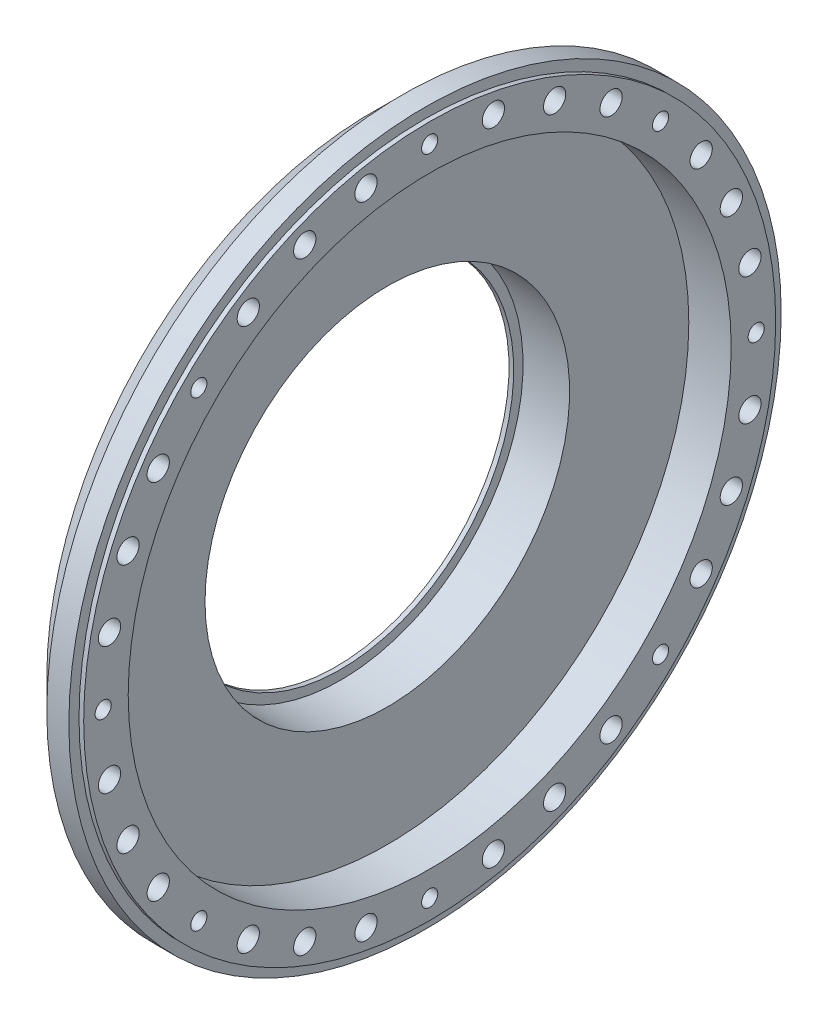
SolidWorks part; units mm, degrees
ref_plane "Front Plane" through (0, 0, 0) normal (0, 0, 1) x (1, 0, 0)
ref_plane "Top Plane" through (0, 0, 0) normal (0, 1, 0) x (1, 0, 0)
ref_plane "Right Plane" through (0, 0, 0) normal (1, 0, 0) x (0, 0, -1)
sketch "Sketch2" plane through (0, 0, 0) normal (0, 0, 1) x (1, 0, 0)
  line L0 (0, 0) -> (58.591, 0) construction
  line L2 (0, 0) -> (18.4, 0)
  line L3 (0, 0) -> (0, 2.5)
  line L4 (0, 2.5) -> (18.4, 2.5)
  line L5 (18.4, 0) -> (18.4, 2.5)
  line L6 (6.0094, 2.5) -> (6.0094, 6)
  line L11 (6.0094, 6) -> (9.9794, 6)
  line L16 (12.9794, 6) -> (12.9794, 3)
  line L17 (12.9794, 3) -> (13.6398, 3)
  line L18 (13.6398, 3) -> (13.6398, 2.5)
  line L19 (13.6398, 2.5) -> (6.0094, 2.5)
  line L22 (13.6398, 2.5) -> (16.1198, 2.5)
  line L23 (13.6398, 2.5) -> (13.6398, 4)
  line L24 (13.6398, 4) -> (16.1198, 4)
  line L25 (16.1198, 2.5) -> (16.1198, 4)
  line L27 (6.0094, 6) -> (9.9794, 6)
  line L28 (6.0094, 6) -> (6.0094, 9)
  line L29 (6.0094, 9) -> (9.9794, 9)
  line L30 (9.9794, 6) -> (9.9794, 9)
  line L31 (6.0094, 9) -> (6.0094, 8.25)
  line L32 (6.0094, 8.25) -> (5.0094, 8.25)
  line L33 (8.6609, 22.001) -> (8.6609, 12.476) construction
  line L34 (5.0094, 12.476) -> (12.3124, 12.476)
  line L35 (9.9794, 9) -> (12.3124, 9)
  line L36 (5.0094, 7.9375) -> (1.7709, 7.9375)
  line L37 (5.0094, 8.25) -> (5.0094, 12.476)
  line L38 (5.0094, 7.9375) -> (5.0094, 13.9365)
  line L39 (5.0094, 13.9365) -> (1.7709, 13.9365)
  line L40 (1.7709, 7.9375) -> (1.7709, 13.9365)
  line L41 (5.0094, 22.001) -> (12.3124, 22.001)
  line L42 (5.0094, 22.001) -> (5.0094, 30.1625)
  line L43 (5.0094, 30.1625) -> (12.3124, 30.1625)
  line L44 (12.3124, 22.001) -> (12.3124, 30.1625)
  line L49 (16.6398, 22.001) -> (16.6398, 7.5)
  line L51 (23.0198, 7.5) -> (23.0198, 6.5)
  line L54 (16.1198, 4) -> (13.6398, 4)
  line L56 (18.0398, 7.5) -> (23.0198, 7.5)
  line L57 (13.3124, 22.001) -> (16.6398, 22.001)
  line L58 (16.1198, 3.5) -> (20.0198, 3.5)
  line L59 (29.9098, 14) -> (26.9098, 11)
  line L60 (4.0094, 31.75) -> (18.0398, 31.75)
  line L61 (18.0398, 7.5) -> (23.0198, 7.5)
  line L62 (18.0398, 7.5) -> (18.0398, 12)
  line L63 (18.0398, 12) -> (23.0198, 12)
  line L64 (23.0198, 7.5) -> (23.0198, 12)
  line L65 (18.0398, 31.75) -> (18.0398, 12)
  line L66 (23.0198, 11) -> (26.9098, 11)
  line L67 (34.8098, 23) -> (31.3098, 19.5)
  line L68 (35.8098, 31) -> (38.7998, 33.99)
  line L69 (29.9098, 14) -> (29.9098, 15)
  line L70 (29.9098, 15) -> (22.9398, 15)
  line L71 (22.9398, 15) -> (21.0398, 15)
  line L72 (18.0398, 7.5) -> (16.6398, 7.5)
  line L73 (21.0398, 15) -> (21.0398, 43)
  line L74 (19.6115, 40) -> (9.6516, 40)
  line L75 (9.6516, 40) -> (4.0094, 40)
  line L76 (21.0398, 43) -> (19.6115, 43)
  line L77 (22.9398, 15) -> (29.9098, 15)
  line L78 (22.9398, 15) -> (22.9398, 21)
  line L79 (22.9398, 21) -> (29.9098, 21)
  line L80 (29.9098, 15) -> (29.9098, 21)
  line L81 (9.6516, 40) -> (19.6115, 40)
  line L82 (9.6516, 40) -> (9.6516, 50)
  line L83 (9.6516, 50) -> (19.6115, 50)
  line L84 (19.6115, 40) -> (19.6115, 50)
  line L85 (4.0094, 40) -> (4.0094, 31.75)
  line L86 (12.9794, 3) -> (12.9794, 2.5)
  line L87 (31.3098, 19.5) -> (29.9098, 19.5)
  line L88 (21.4694, 63.5) -> (21.4694, 51.308)
  line L89 (21.4694, 63.5) -> (25.9398, 63.5)
  line L90 (25.9398, 63.5) -> (25.9398, 25)
  line L91 (27.8398, 25) -> (25.9398, 25)
  line L92 (9.6516, 48) -> (8.2233, 48)
  line L93 (8.2233, 48) -> (8.2233, 53.476)
  line L94 (8.2233, 53.476) -> (19.6115, 53.476)
  line L95 (19.6115, 53.476) -> (19.6115, 50)
  line L96 (13.9174, 63.001) -> (13.9174, 53.476) construction
  line L97 (8.2233, 63.001) -> (19.6115, 63.001)
  line L98 (8.2233, 63.001) -> (8.2233, 68.2625)
  line L99 (8.2233, 68.2625) -> (19.6115, 68.2625)
  line L100 (19.6115, 63.001) -> (19.6115, 68.2625)
  line L101 (12.9794, 6) -> (11.9794, 6)
  line L102 (8.2233, 44.825) -> (4.9848, 44.825)
  line L103 (8.2233, 44.825) -> (8.2233, 54.9365)
  line L104 (8.2233, 54.9365) -> (4.9848, 54.9365)
  line L106 (9.9794, 6) -> (10.8794, 6)
  line L107 (27.8398, 25) -> (34.8098, 25)
  line L108 (34.8098, 25) -> (34.8098, 23)
  line L109 (0, 0) -> (-2, 0)
  line L110 (0, 0) -> (0, 11)
  line L111 (27.8398, 25) -> (34.8098, 25)
  line L112 (27.8398, 25) -> (27.8398, 32.5)
  line L113 (27.8398, 32.5) -> (34.8098, 32.5)
  line L114 (34.8098, 25) -> (34.8098, 32.5)
  line L115 (35.8098, 31) -> (34.8098, 31)
  line L116 (27.8398, 32.5) -> (27.8398, 64.5)
  line L117 (20.5849, 74.025) -> (6.2499, 74.025)
  line L118 (6.2499, 74.025) -> (6.2499, 76.2)
  line L119 (38.7998, 47.29) -> (30.8398, 55.25)
  line L120 (0, 11) -> (-2, 11)
  line L121 (38.7998, 43.815) -> (30.8623, 43.815)
  line L123 (-4.8152, 69.85) -> (1.5348, 76.2)
  line L124 (38.7998, 47.29) -> (38.7998, 33.99)
  line L125 (-2, 0) -> (-2, 11)
  line L126 (38.7998, 37.465) -> (30.8623, 37.465)
  line L127 (30.8623, 43.815) -> (30.8623, 37.465)
  line L128 (6.0094, 2.5) -> (6.0094, 0)
  line L129 (-0.0152, 63.5) -> (-0.0152, 30)
  line L132 (4.9848, 63.5) -> (-0.0152, 63.5)
  line L136 (-1.8152, 30) -> (-11.7752, 30)
  line L138 (-13.7752, 25.4) -> (-2, 25.4)
  line L139 (-2, 25.4) -> (-2, 11.5)
  line L140 (27.8398, 64.5) -> (20.5849, 64.5)
  line L141 (-1.8152, 30) -> (-11.7752, 30)
  line L142 (-1.8152, 30) -> (-1.8152, 39)
  line L143 (-1.8152, 39) -> (-11.7752, 39)
  line L144 (-11.7752, 30) -> (-11.7752, 39)
  line L145 (20.5849, 64.5) -> (20.5849, 74.025)
  line L146 (-12.7752, 37) -> (-12.7752, 47.29)
  line L147 (-12.7752, 37) -> (-11.7752, 37)
  line L148 (30.8398, 55.25) -> (30.8398, 76.2)
  line L149 (11.9794, 6) -> (11.9794, 5.45)
  line L154 (-2, 11.5) -> (0.5, 11.5)
  line L155 (4.9848, 60.6197) -> (24.0348, 60.6197)
  line L160 (4.9848, 60.6197) -> (4.9848, 55.8572)
  line L161 (4.9848, 55.8572) -> (24.0348, 55.8572)
  line L166 (24.0348, 60.6197) -> (24.0348, 55.8572)
  line L167 (4.9848, 60.6197) -> (24.0348, 55.8572) construction
  line L172 (4.9848, 55.8572) -> (24.0348, 60.6197) construction
  line L173 (24.0348, 62.2072) -> (25.9398, 62.2072)
  line L174 (11.9794, 5.45) -> (10.8794, 5.45)
  line L175 (10.8794, 6) -> (10.8794, 5.45)
  line L176 (24.0348, 62.2072) -> (24.0348, 54.2697)
  line L177 (24.0348, 54.2697) -> (25.9398, 54.2697)
  line L178 (25.9398, 62.2072) -> (25.9398, 54.2697)
  line L179 (24.0348, 62.2072) -> (25.9398, 54.2697) construction
  line L180 (24.0348, 54.2697) -> (25.9398, 62.2072) construction
  line L181 (3, 19.6197) -> (15.7, 19.6197)
  line L182 (3, 19.6197) -> (3, 14.8572)
  line L183 (3, 14.8572) -> (15.7, 14.8572)
  line L184 (15.7, 19.6197) -> (15.7, 14.8572)
  line L185 (3, 19.6197) -> (15.7, 14.8572) construction
  line L186 (3, 14.8572) -> (15.7, 19.6197) construction
  line L187 (15.7, 21.2072) -> (16.6398, 21.2072)
  line L188 (15.7, 21.2072) -> (15.7, 13.2697)
  line L189 (15.7, 13.2697) -> (16.6398, 13.2697)
  line L190 (16.6398, 21.2072) -> (16.6398, 13.2697)
  line L191 (15.7, 21.2072) -> (16.6398, 13.2697) construction
  line L192 (15.7, 13.2697) -> (16.6398, 21.2072) construction
  line L193 (0.5, 11.5) -> (0.5, 6.9375)
  line L194 (0.5, 6.9375) -> (1.7709, 6.9375)
  line L195 (23.0198, 6.5) -> (20.0198, 3.5)
  line L196 (4.9848, 63.5) -> (4.9848, 54.9365)
  line L197 (3, 43.825) -> (4.9848, 43.825)
  line L198 (1.7709, 6.9375) -> (1.7709, 7.9375)
  line L199 (6.0094, 0) -> (12.9794, 0)
  line L200 (12.9794, 0) -> (12.9794, 2.5)
  line L201 (18.0398, 31.75) -> (18.0398, 35.875)
  line L202 (18.0398, 35.875) -> (21.0398, 35.875)
  line L203 (30.8398, 76.2) -> (6.2499, 76.2)
  line L204 (2.8049, 69.85) -> (7.2499, 69.85) construction
  line L205 (7.2499, 67.4688) -> (26.2999, 67.4688)
  line L206 (7.2499, 74.025) -> (7.2499, 64.5)
  line L207 (7.2499, 64.5) -> (-1.8152, 64.5)
  line L208 (-1.8152, 64.5) -> (-1.8152, 39)
  line L209 (-12.7752, 47.29) -> (-4.8152, 55.25)
  line L210 (-4.8152, 55.25) -> (-4.8152, 69.85)
  line L211 (7.2499, 67.4688) -> (7.2499, 72.2312)
  line L212 (7.2499, 72.2312) -> (26.2999, 72.2313)
  line L213 (26.2999, 67.4688) -> (26.2999, 72.2313)
  line L214 (26.2999, 73.8187) -> (30.8398, 73.8187)
  line L215 (26.2999, 73.8187) -> (26.2999, 65.8813)
  line L216 (26.2999, 65.8813) -> (30.8398, 65.8813)
  line L217 (30.8398, 73.8187) -> (30.8398, 65.8813)
  line L218 (2.8049, 72.2313) -> (25.0299, 72.2313)
  line L219 (2.8049, 72.2313) -> (2.8049, 67.4687)
  line L220 (2.8049, 67.4687) -> (25.0299, 67.4687)
  line L221 (25.0299, 72.2313) -> (25.0299, 67.4687)
  line L222 (25.0299, 69.85) -> (20.5849, 69.85) construction
  line L223 (21.4694, 51.308) -> (22.9398, 51.308)
  line L224 (22.9398, 51.308) -> (22.9398, 21)
  line L225 (13.6398, 4) -> (13.6398, 12.2697)
  line L226 (13.6398, 12.2697) -> (13.3124, 12.2697)
  line L227 (13.3124, 12.2697) -> (13.3124, 22.001)
  line L228 (12.3124, 9) -> (12.3124, 12.476)
  line L229 (-1.8152, 30) -> (-0.0152, 30)
  line L230 (8.2233, 65.6317) -> (2.8049, 65.6317) construction
  line L231 (19.6115, 65.6317) -> (25.0299, 65.6317) construction
  line L232 (1.5348, 76.2) -> (6.2499, 76.2)
  line L233 (-11.7752, 30) -> (-13.7752, 30)
  line L234 (-13.7752, 30) -> (-13.7752, 25.4)
  line L235 (3, 13.9365) -> (3, 43.825)
  line L236 (4.9848, 54.9365) -> (4.9848, 44.825)
  line L237 (4.9848, 43.825) -> (4.9848, 44.825)
  circle A0 centre (26.8898, 25.95) radius 0.95
  circle A1 centre (21.9898, 15.95) radius 0.95
  circle A2 centre (17.3398, 8.2) radius 0.7
  circle A3 centre (10.4294, 6.45) radius 0.45
  circle A4 centre (-0.9152, 30.9) radius 0.9
  point P7 (24.9873, 58.2385)
  point P131 (16.1699, 17.2385)
  point P135 (14.5098, 58.2385)
  point P146 (9.35, 17.2385)
sketch "Sketch3" plane through (0, 0, 0) normal (1, 0, 0) x (0, 0, -1)
  line L0 (0, 0) -> (0, 69.85) construction
  line L1 (0, 0) -> (13.6271, 68.5079) construction
  line L2 (0, 0) -> (0, 58.2385) construction
  line L3 (0, 0) -> (50.436, 29.1192) construction
  line L4 (0, 0) -> (0, 31.75) construction
  line L5 (0, 0) -> (12.1502, 29.3332) construction
  line L6 (0, 0) -> (0, 17.2385) construction
  line L7 (0, 0) -> (14.929, 8.6192) construction
  line L8 (0, 0) -> (0, 58.2385) construction
  line L9 (0, 0) -> (50.436, 29.1192) construction
  line L10 (0, 0) -> (5.9583, 29.9542) construction
  line L11 (0, 0) -> (16.9677, 25.394) construction
  circle A0 centre (0, 0) radius 69.85 construction
  circle A1 centre (0, 0) radius 58.2385 construction
  circle A2 centre (0, 0) radius 31.75 construction
  circle A3 centre (0, 0) radius 17.2385 construction
  circle A4 centre (0, 69.85) radius 3.175
  circle A5 centre (0, 58.2385) radius 4.7625
  circle A6 centre (0, 31.75) radius 3.175
  circle A7 centre (0, 17.2385) radius 4.7625
  circle A8 centre (13.6271, 68.5079) radius 3.175
  circle A9 centre (26.7304, 64.533) radius 3.175
  circle A10 centre (38.8066, 58.0782) radius 3.175
  circle A11 centre (49.3914, 49.3914) radius 3.175
  circle A12 centre (58.0782, 38.8066) radius 3.175
  circle A13 centre (64.533, 26.7304) radius 3.175
  circle A14 centre (68.5079, 13.6271) radius 3.175
  circle A15 centre (69.85, 0) radius 3.175
  circle A16 centre (68.5079, -13.6271) radius 3.175
  circle A17 centre (64.533, -26.7304) radius 3.175
  circle A18 centre (58.0782, -38.8066) radius 3.175
  circle A19 centre (49.3914, -49.3914) radius 3.175
  circle A20 centre (38.8066, -58.0782) radius 3.175
  circle A21 centre (26.7304, -64.533) radius 3.175
  circle A22 centre (13.6271, -68.5079) radius 3.175
  circle A23 centre (0, -69.85) radius 3.175
  circle A24 centre (-13.6271, -68.5079) radius 3.175
  circle A25 centre (-26.7304, -64.533) radius 3.175
  circle A26 centre (-38.8066, -58.0782) radius 3.175
  circle A27 centre (-49.3914, -49.3914) radius 3.175
  circle A28 centre (-58.0782, -38.8066) radius 3.175
  circle A29 centre (-64.533, -26.7304) radius 3.175
  circle A30 centre (-68.5079, -13.6271) radius 3.175
  circle A31 centre (-69.85, 0) radius 3.175
  circle A32 centre (-68.5079, 13.6271) radius 3.175
  circle A33 centre (-64.533, 26.7304) radius 3.175
  circle A34 centre (-58.0782, 38.8066) radius 3.175
  circle A35 centre (-49.3914, 49.3914) radius 3.175
  circle A36 centre (-38.8066, 58.0782) radius 3.175
  circle A37 centre (-26.7304, 64.533) radius 3.175
  circle A38 centre (-13.6271, 68.5079) radius 3.175
  circle A47 centre (50.436, 29.1192) radius 4.7625
  circle A48 centre (50.436, -29.1192) radius 4.7625
  circle A49 centre (0, -58.2385) radius 4.7625
  circle A50 centre (-50.436, -29.1192) radius 4.7625
  circle A51 centre (-50.436, 29.1192) radius 4.7625
  circle A58 centre (12.1502, 29.3332) radius 3.175
  circle A59 centre (22.4506, 22.4506) radius 3.175
  circle A60 centre (29.3332, 12.1502) radius 3.175
  circle A61 centre (31.75, 0) radius 3.175
  circle A62 centre (29.3332, -12.1502) radius 3.175
  circle A63 centre (22.4506, -22.4506) radius 3.175
  circle A64 centre (12.1502, -29.3332) radius 3.175
  circle A65 centre (0, -31.75) radius 3.175
  circle A66 centre (-12.1502, -29.3332) radius 3.175
  circle A67 centre (-22.4506, -22.4506) radius 3.175
  circle A68 centre (-29.3332, -12.1502) radius 3.175
  circle A69 centre (-31.75, 0) radius 3.175
  circle A70 centre (-29.3332, 12.1502) radius 3.175
  circle A71 centre (-22.4506, 22.4506) radius 3.175
  circle A72 centre (14.929, 8.6192) radius 4.7625
  circle A73 centre (14.929, -8.6192) radius 4.7625
  circle A74 centre (0, -17.2385) radius 4.7625
  circle A75 centre (-14.929, -8.6192) radius 4.7625
  circle A76 centre (-14.929, 8.6192) radius 4.7625
  circle A77 centre (0, 0) radius 50
  circle A78 centre (0, 0) radius 9
  circle A79 centre (-12.1502, 29.3332) radius 3.175
  circle A80 centre (0, 0) radius 76.2
  circle A81 centre (0, 0) radius 74.025
  circle A82 centre (0, 69.85) radius 3.9687
  circle A83 centre (49.3914, 49.3914) radius 3.9687
  circle A84 centre (69.85, 0) radius 3.9688
  circle A85 centre (49.3914, -49.3914) radius 3.9687
  circle A86 centre (0, -69.85) radius 3.9687
  circle A87 centre (-49.3914, -49.3914) radius 3.9687
  circle A88 centre (-69.85, 0) radius 3.9688
  circle A89 centre (-49.3914, 49.3914) radius 3.9687
  circle A90 centre (0, 69.85) radius 2.3812
  circle A91 centre (13.6271, 68.5079) radius 2.3812
  circle A92 centre (26.7304, 64.533) radius 2.3813
  circle A93 centre (38.8066, 58.0782) radius 2.3812
  circle A94 centre (49.3914, 49.3914) radius 2.3812
  circle A95 centre (58.0782, 38.8066) radius 2.3812
  circle A96 centre (64.533, 26.7304) radius 2.3813
  circle A97 centre (68.5079, 13.6271) radius 2.3813
  circle A98 centre (69.85, 0) radius 2.3813
  circle A99 centre (68.5079, -13.6271) radius 2.3813
  circle A100 centre (64.533, -26.7304) radius 2.3813
  circle A101 centre (58.0782, -38.8066) radius 2.3812
  circle A102 centre (49.3914, -49.3914) radius 2.3812
  circle A103 centre (38.8066, -58.0782) radius 2.3812
  circle A104 centre (26.7304, -64.533) radius 2.3813
  circle A105 centre (13.6271, -68.5079) radius 2.3812
  circle A106 centre (0, -69.85) radius 2.3812
  circle A107 centre (-13.6271, -68.5079) radius 2.3812
  circle A108 centre (-26.7304, -64.533) radius 2.3813
  circle A109 centre (-38.8066, -58.0782) radius 2.3812
  circle A110 centre (-49.3914, -49.3914) radius 2.3812
  circle A111 centre (-58.0782, -38.8066) radius 2.3812
  circle A112 centre (-64.533, -26.7304) radius 2.3812
  arc A113 (3.0399, 30.8338) -> (8.9911, 29.65) centre (5.9583, 29.9542) cw
  arc A114 (14.6081, 27.3234) -> (19.6532, 23.9523) centre (16.9677, 25.394) cw
  arc A115 (23.9523, 19.6532) -> (27.3234, 14.6081) centre (25.394, 16.9677) cw
  arc A116 (29.65, 8.9911) -> (30.8338, 3.0399) centre (29.9542, 5.9583) cw
  arc A117 (30.8338, -3.0399) -> (29.65, -8.9911) centre (29.9542, -5.9583) cw
  arc A118 (27.3234, -14.6081) -> (23.9523, -19.6532) centre (25.394, -16.9677) cw
  arc A119 (19.6532, -23.9523) -> (14.6081, -27.3234) centre (16.9677, -25.394) cw
  arc A120 (8.9911, -29.65) -> (3.0399, -30.8338) centre (5.9583, -29.9542) cw
  arc A121 (-3.0399, -30.8338) -> (-8.9911, -29.65) centre (-5.9583, -29.9542) cw
  arc A122 (-14.6081, -27.3234) -> (-19.6532, -23.9523) centre (-16.9677, -25.394) cw
  arc A123 (-23.9523, -19.6532) -> (-27.3234, -14.6081) centre (-25.394, -16.9677) cw
  arc A124 (-29.65, -8.9911) -> (-30.8338, -3.0399) centre (-29.9542, -5.9583) cw
  arc A125 (-30.8338, 3.0399) -> (-29.65, 8.9911) centre (-29.9542, 5.9583) cw
  arc A126 (-27.3234, 14.6081) -> (-23.9523, 19.6532) centre (-25.394, 16.9677) cw
  arc A127 (-19.6532, 23.9523) -> (-14.6081, 27.3234) centre (-16.9677, 25.394) cw
  arc A128 (-8.9911, 29.65) -> (-3.0399, 30.8338) centre (-5.9583, 29.9542) cw
  arc A129 (26.9875, 0) -> (26.9932, 0.1932) centre (30.2705, 0) cw
  arc A130 (65.0988, 0.2771) -> (65.0875, 0) centre (68.4964, 0) ccw
  circle A131 centre (1.5875, 0) radius 40
  circle A132 centre (1.5875, 0) radius 2.5
  circle A133 centre (1.5875, 0) radius 3
  circle A134 centre (1.5875, 0) radius 43
  circle A135 centre (-68.5079, -13.6271) radius 2.3813
  circle A136 centre (-69.85, 0) radius 2.3813
  circle A137 centre (-68.5079, 13.6271) radius 2.3813
  circle A138 centre (-64.533, 26.7304) radius 2.3812
  circle A139 centre (-58.0782, 38.8066) radius 2.3812
  circle A140 centre (-49.3914, 49.3914) radius 2.3812
  circle A141 centre (-38.8066, 58.0782) radius 2.3812
  circle A142 centre (-26.7304, 64.533) radius 2.3813
  circle A143 centre (-13.6271, 68.5079) radius 2.3812
  circle A144 centre (0, 58.2385) radius 2.3812
  circle A145 centre (0, 58.2385) radius 3.9688
  circle A146 centre (50.436, 29.1192) radius 3.9688
  circle A147 centre (50.436, 29.1192) radius 2.3813
  circle A148 centre (50.436, -29.1192) radius 3.9687
  circle A149 centre (50.436, -29.1192) radius 2.3812
  circle A150 centre (0, -58.2385) radius 3.9687
  circle A151 centre (0, -58.2385) radius 2.3812
  circle A152 centre (-50.436, -29.1192) radius 3.9687
  circle A153 centre (-50.436, -29.1192) radius 2.3812
  circle A154 centre (-50.436, 29.1192) radius 3.9687
  circle A155 centre (-50.436, 29.1192) radius 2.3812
  spline S1 degree 4 number of poles 499 (26.9875, 0) -> (26.9932, 0.1932)
  spline S3 degree 4 number of poles 617 (65.0875, 0) -> (65.0988, 0.2771)
  point P116 (0, 0)
  point P225 (0, 0)
sketch "Sketch4" plane through (0, 0, 0) normal (0, 0, 1) x (1, 0, 0)
  line L0 (20.5849, 74.025) -> (6.2499, 74.025) construction
  line L1 (6.2499, 74.025) -> (6.2499, 76.2) construction
  line L2 (7.2499, 74.025) -> (7.2499, 64.5) construction
  line L3 (7.2499, 64.5) -> (-1.8152, 64.5) construction
  line L4 (-1.8152, 64.5) -> (-1.8152, 39) construction
  line L5 (-11.7752, 30) -> (-11.7752, 39) construction
  line L6 (-1.8152, 39) -> (-11.7752, 39) construction
  line L7 (-12.7752, 37) -> (-11.7752, 37) construction
  line L8 (-12.7752, 37) -> (-12.7752, 47.29) construction
  line L9 (-12.7752, 47.29) -> (-4.8152, 55.25) construction
  line L10 (-4.8152, 55.25) -> (-4.8152, 69.85) construction
  line L12 (7.2499, 74.025) -> (6.2499, 74.025)
  line L13 (6.2499, 74.025) -> (6.2499, 76.2)
  line L14 (7.2499, 74.025) -> (7.2499, 64.5)
  line L15 (7.2499, 64.5) -> (-1.8152, 64.5)
  line L16 (-1.8152, 64.5) -> (-1.8152, 39)
  line L17 (-11.7752, 37) -> (-11.7752, 39)
  line L18 (-1.8152, 39) -> (-11.7752, 39)
  line L19 (-12.7752, 37) -> (-11.7752, 37)
  line L20 (-12.7752, 37) -> (-12.7752, 47.29)
  line L21 (-12.7752, 47.29) -> (-4.8152, 55.25)
  line L22 (-4.8152, 55.25) -> (-4.8152, 69.85)
  line L24 (-4.8152, 69.85) -> (1.5348, 76.2) construction
  line L25 (1.5348, 76.2) -> (6.2499, 76.2) construction
  line L26 (-4.8152, 69.85) -> (1.5348, 76.2)
  line L27 (1.5348, 76.2) -> (6.2499, 76.2)
revolve "Revolve1" add sketch "Sketch4" angle 360 about L0
sketch "Sketch5" plane through (7.2499, 0, 0) normal (1, 0, 0) x (0, 0, -1)
  circle A0 centre (13.6271, 68.5079) radius 2.3812 construction
  circle A1 centre (26.7304, 64.533) radius 2.3813 construction
  circle A2 centre (38.8066, 58.0782) radius 2.3813 construction
  circle A3 centre (58.0782, 38.8066) radius 2.3812 construction
  circle A4 centre (64.533, 26.7304) radius 2.3813 construction
  circle A5 centre (68.5079, 13.6271) radius 2.3813 construction
  circle A6 centre (68.5079, -13.6271) radius 2.3813 construction
  circle A7 centre (64.533, -26.7304) radius 2.3813 construction
  circle A8 centre (58.0782, -38.8066) radius 2.3813 construction
  circle A9 centre (38.8066, -58.0782) radius 2.3812 construction
  circle A10 centre (26.7304, -64.533) radius 2.3813 construction
  circle A11 centre (13.6271, -68.5079) radius 2.3812 construction
  circle A12 centre (-13.6271, -68.5079) radius 2.3812 construction
  circle A13 centre (-26.7304, -64.533) radius 2.3813 construction
  circle A14 centre (-38.8066, -58.0782) radius 2.3812 construction
  circle A15 centre (-58.0782, -38.8066) radius 2.3812 construction
  circle A16 centre (-64.533, -26.7304) radius 2.3813 construction
  circle A17 centre (-68.5079, -13.6271) radius 2.3813 construction
  circle A18 centre (-68.5079, 13.6271) radius 2.3813 construction
  circle A19 centre (-64.533, 26.7304) radius 2.3813 construction
  circle A20 centre (-58.0782, 38.8066) radius 2.3813 construction
  circle A21 centre (-38.8066, 58.0782) radius 2.3812 construction
  circle A22 centre (-26.7304, 64.533) radius 2.3813 construction
  circle A23 centre (-13.6271, 68.5079) radius 2.3812 construction
  circle A24 centre (13.6271, 68.5079) radius 2.3812
  circle A25 centre (26.7304, 64.533) radius 2.3813
  circle A26 centre (38.8066, 58.0782) radius 2.3812
  circle A27 centre (58.0782, 38.8066) radius 2.3812
  circle A28 centre (64.533, 26.7304) radius 2.3813
  circle A29 centre (68.5079, 13.6271) radius 2.3813
  circle A30 centre (68.5079, -13.6271) radius 2.3813
  circle A31 centre (64.533, -26.7304) radius 2.3813
  circle A32 centre (58.0782, -38.8066) radius 2.3812
  circle A33 centre (38.8066, -58.0782) radius 2.3812
  circle A34 centre (26.7304, -64.533) radius 2.3813
  circle A35 centre (13.6271, -68.5079) radius 2.3812
  circle A36 centre (-13.6271, -68.5079) radius 2.3812
  circle A37 centre (-26.7304, -64.533) radius 2.3813
  circle A38 centre (-38.8066, -58.0782) radius 2.3812
  circle A39 centre (-58.0782, -38.8066) radius 2.3812
  circle A40 centre (-64.533, -26.7304) radius 2.3812
  circle A41 centre (-68.5079, -13.6271) radius 2.3813
  circle A42 centre (-68.5079, 13.6271) radius 2.3813
  circle A43 centre (-64.533, 26.7304) radius 2.3812
  circle A44 centre (-58.0782, 38.8066) radius 2.3812
  circle A45 centre (-38.8066, 58.0782) radius 2.3812
  circle A46 centre (-26.7304, 64.533) radius 2.3813
  circle A47 centre (-13.6271, 68.5079) radius 2.3812
extrude "Cut-Extrude1" cut sketch "Sketch5" against normal up to vertex (4.445 mm away) up to point (2.8049, 72.2313, 0)
sketch "Sketch6" plane through (7.2499, 0, 0) normal (1, 0, 0) x (0, 0, -1)
  circle A0 centre (49.3914, -49.3914) radius 3.9688 construction
  circle A1 centre (0, 0) radius 74.025
  circle A2 centre (0, 0) radius 74.025
  circle A3 centre (69.85, 0) radius 3.9688 construction
  circle A4 centre (49.3914, 49.3914) radius 3.9687 construction
  circle A5 centre (0, 69.85) radius 3.9687 construction
  circle A6 centre (-49.3914, 49.3914) radius 3.9687 construction
  circle A7 centre (-69.85, 0) radius 3.9688 construction
  circle A8 centre (-49.3914, -49.3914) radius 3.9688 construction
  circle A9 centre (0, -69.85) radius 3.9687 construction
  circle A10 centre (49.3914, -49.3914) radius 3.9687
  circle A11 centre (69.85, 0) radius 3.9688
  circle A12 centre (49.3914, 49.3914) radius 3.9687
  circle A13 centre (0, 69.85) radius 3.9687
  circle A14 centre (-49.3914, 49.3914) radius 3.9687
  circle A15 centre (-69.85, 0) radius 3.9688
  circle A16 centre (-49.3914, -49.3914) radius 3.9687
  circle A17 centre (0, -69.85) radius 3.9687
  circle A18 centre (0, 69.85) radius 1.7272
  circle A19 centre (49.3914, 49.3914) radius 1.7272
  circle A20 centre (69.85, 0) radius 1.7272
  circle A21 centre (49.3914, -49.3914) radius 1.7272
  circle A22 centre (0, -69.85) radius 1.7272
  circle A23 centre (-49.3914, -49.3914) radius 1.7272
  circle A24 centre (-69.85, 0) radius 1.7272
  circle A25 centre (-49.3914, 49.3914) radius 1.7272
  dimension "D2" = 3.4544
  dimension "D1" = 0
extrude "Cut-Extrude2" cut sketch "Sketch6" against normal blind 9.525 contours A18 | A25 | A24 | A23 | A22 | A21 | A20 | A19
